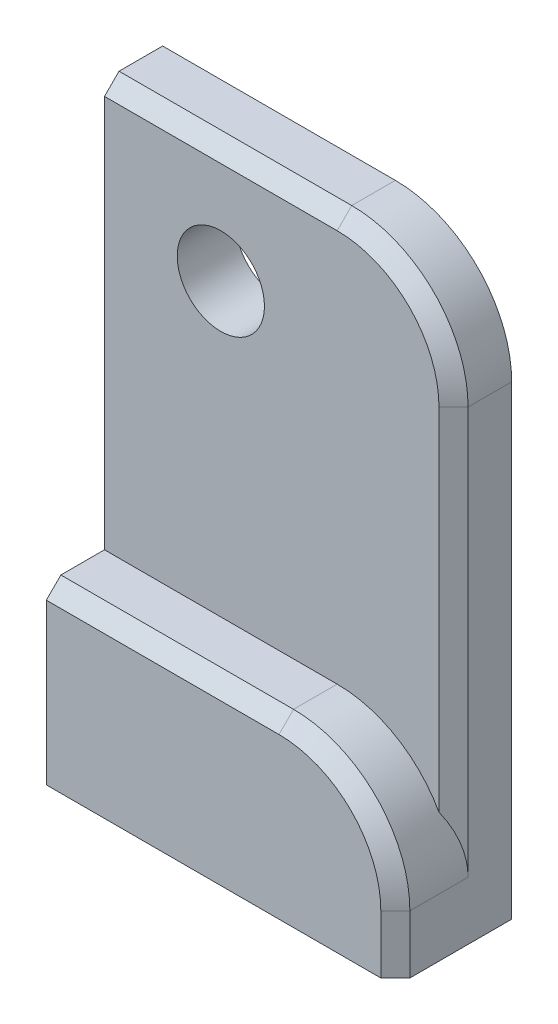
SolidWorks part; units mm, degrees
ref_plane "Front Plane" through (0, 0, 0) normal (0, 0, 1) x (1, 0, 0)
ref_plane "Top Plane" through (0, 0, 0) normal (0, 1, 0) x (1, 0, 0)
ref_plane "Right Plane" through (0, 0, 0) normal (1, 0, 0) x (0, 0, -1)
sketch "Sketch1" plane through (0, 0, 0) normal (0, 0, 1) x (1, 0, 0)
  line L1 (0, 0) -> (60, 0)
  line L2 (0, 0) -> (0, 100)
  line L3 (0, 100) -> (60, 100)
  line L4 (60, 0) -> (60, 100)
  dimension "D1" = 100
  dimension "D2" = 60
extrude "Boss-Extrude2" add sketch "Sketch1" along normal blind 10
sketch "Sketch4" plane through (0, 0, 10) normal (0, 0, 1) x (1, 0, 0)
  line L0 (60, 0) -> (60, 100) construction
  line L1 (0, 0) -> (60, 0)
  line L2 (0, 0) -> (0, 30)
  line L3 (0, 30) -> (60, 30)
  line L4 (60, 0) -> (60, 30)
  dimension "D1" = 30
extrude "Boss-Extrude3" add sketch "Sketch4" along normal blind 10
sketch "Sketch5" plane through (0, 0, 10) normal (0, 0, 1) x (1, 0, 0)
  line L0 (60, 100) -> (0, 100) construction
  line L1 (0, 100) -> (0, 30) construction
  circle A0 centre (20, 80) radius 7.5
  dimension "D1" = 15
  dimension "D2" = 20
  dimension "D3" = 20
extrude "Cut-Extrude1" cut sketch "Sketch5" against normal through all
fillet "Fillet1" radius 20 2 edges at (60, 30, 15) (60, 100, 5)
chamfer "Chamfer1" distance 2.5 angle 45 6 edges at (60, 5, 20) (54.1421, 24.1421, 20) (20, 30, 20) (60, 45, 10) (54.1421, 94.1421, 10) (20, 100, 10)
shell "Shell3" thickness 2
